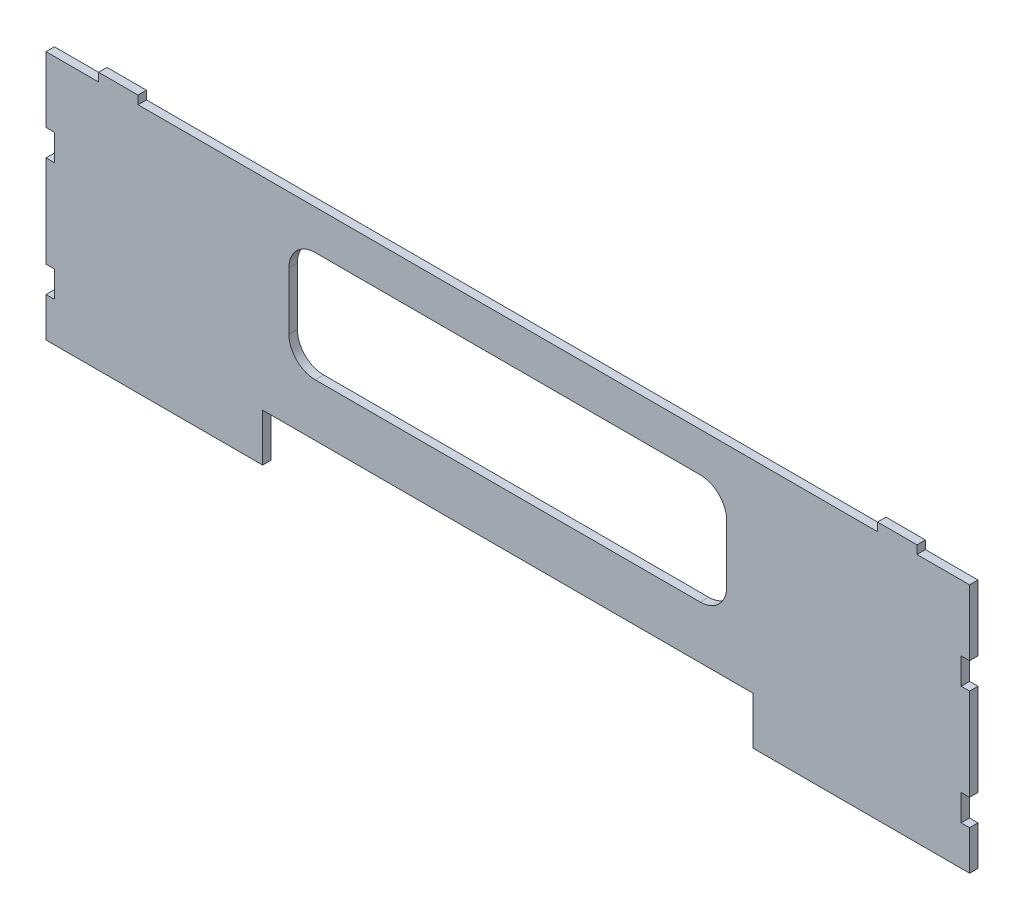
SolidWorks part; units mm, degrees
ref_plane "Front Plane" through (0, 0, 0) normal (0, 0, 1) x (1, 0, 0)
ref_plane "Top Plane" through (0, 0, 0) normal (0, 1, 0) x (1, 0, 0)
ref_plane "Right Plane" through (0, 0, 0) normal (1, 0, 0) x (0, 0, -1)
sketch "Sketch1" plane through (0, 0, 0) normal (0, 0, 1) x (1, 0, 0)
  line L0 (-118.4275, -120.65) -> (-118.4275, -97.663)
  line L1 (-223.0755, 0) -> (-197.6755, 0)
  line L2 (-223.0755, 0) -> (-223.0755, -120.65)
  line L3 (-223.0755, -120.65) -> (-118.4275, -120.65)
  line L4 (223.0755, 0) -> (223.0755, -120.65)
  line L5 (-118.4275, -97.663) -> (118.4275, -97.663)
  line L6 (118.4275, -97.663) -> (118.4275, -120.65)
  line L7 (118.4275, -120.65) -> (223.0755, -120.65)
  line L8 (-197.6755, 0) -> (-197.6755, 4.064)
  line L9 (-197.6755, 4.064) -> (-178.6255, 4.064)
  line L10 (-178.6255, 4.064) -> (-178.6255, 0)
  line L11 (178.6255, 0) -> (178.6255, 4.064)
  line L12 (178.6255, 4.064) -> (197.6755, 4.064)
  line L13 (197.6755, 4.064) -> (197.6755, 0)
  line L14 (-178.6255, 0) -> (178.6255, 0)
  line L15 (197.6755, 0) -> (223.0755, 0)
  line L16 (-223.0755, 4.064) -> (-223.0755, 0) construction
  line L17 (223.0755, 4.064) -> (223.0755, 0) construction
  line L18 (118.4275, -123.063) -> (118.4275, -97.663) construction
  line L19 (-118.4275, -97.663) -> (118.4275, -97.663) construction
  line L20 (-115.8875, -120.65) -> (115.8875, -120.65) construction
  line L21 (-118.4275, -123.063) -> (-118.4275, -97.663) construction
  line L22 (178.6255, 4.064) -> (197.6755, 4.064) construction
  line L23 (-197.6755, 4.064) -> (-197.6755, 0) construction
  line L24 (-178.6255, 4.064) -> (-178.6255, 0) construction
  line L25 (178.6255, 4.064) -> (178.6255, 0) construction
  line L26 (197.6755, 4.064) -> (197.6755, 0) construction
  line L27 (197.6755, 0) -> (223.0755, 0) construction
extrude "Boss-Extrude1" add sketch "Sketch1" along normal blind 4.064
sketch "Sketch2" plane through (0, 0, 4.064) normal (0, 0, 1) x (1, 0, 0)
  line L0 (-223.0755, 0) -> (-223.0755, -120.65) construction
  line L1 (-223.0755, -31.75) -> (-219.0115, -31.75)
  line L2 (-223.0755, -31.75) -> (-223.0755, -44.45)
  line L3 (-223.0755, -44.45) -> (-219.0115, -44.45)
  line L4 (-219.0115, -31.75) -> (-219.0115, -44.45)
  line L6 (-223.0755, -88.9) -> (-219.0115, -88.9)
  line L7 (-223.0755, -88.9) -> (-223.0755, -101.6)
  line L8 (-223.0755, -101.6) -> (-219.0115, -101.6)
  line L9 (-219.0115, -88.9) -> (-219.0115, -101.6)
  line L10 (-223.0755, -120.65) -> (-118.4275, -120.65) construction
  line L11 (-223.0755, 0) -> (-197.6755, 0) construction
  line L12 (0, 0) -> (0, -165.7208) construction
  line L13 (219.0115, -88.9) -> (219.0115, -101.6)
  line L14 (223.0755, -101.6) -> (219.0115, -101.6)
  line L15 (223.0755, -88.9) -> (223.0755, -101.6)
  line L16 (223.0755, -88.9) -> (219.0115, -88.9)
  line L17 (219.0115, -31.75) -> (219.0115, -44.45)
  line L18 (223.0755, -44.45) -> (219.0115, -44.45)
  line L19 (223.0755, -31.75) -> (223.0755, -44.45)
  line L20 (223.0755, -31.75) -> (219.0115, -31.75)
  dimension "D1" = 4.064
  dimension "D2" = 19.05
  dimension "D3" = 12.7
  dimension "D4" = 31.75
  dimension "D5" = 12.7
extrude "Cut-Extrude1" cut sketch "Sketch2" against normal through all
sketch "Sketch3" plane through (0, 0, 4.064) normal (0, 0, 1) x (1, 0, 0)
  line L0 (-118.4275, -97.663) -> (118.4275, -97.663) construction
  line L1 (-93.0275, -19.05) -> (93.0275, -19.05)
  line L2 (-105.7275, -31.75) -> (-105.7275, -59.563)
  line L3 (-93.0275, -72.263) -> (93.0275, -72.263)
  line L4 (105.7275, -31.75) -> (105.7275, -59.563)
  line L5 (-178.6255, 0) -> (178.6255, 0) construction
  line L6 (118.4275, -123.063) -> (118.4275, -97.663) construction
  arc A0 (-105.7275, -59.563) -> (-93.0275, -72.263) centre (-93.0275, -59.563) ccw
  arc A1 (93.0275, -72.263) -> (105.7275, -59.563) centre (93.0275, -59.563) ccw
  arc A2 (93.0275, -19.05) -> (105.7275, -31.75) centre (93.0275, -31.75) cw
  arc A3 (-93.0275, -19.05) -> (-105.7275, -31.75) centre (-93.0275, -31.75) ccw
  point P8 (0, -19.05)
  dimension "D4" = 12.7
  dimension "D1" = 25.4
  dimension "D2" = 19.05
  dimension "D3" = 12.7
extrude "Cut-Extrude2" cut sketch "Sketch3" against normal through all
